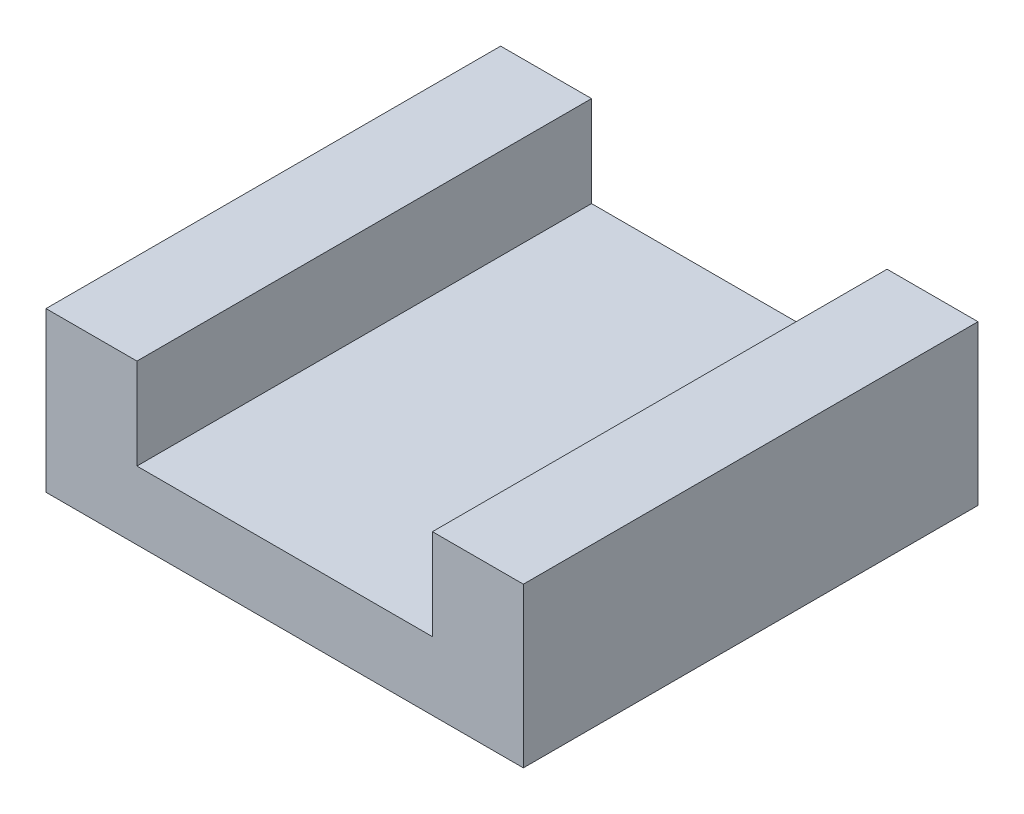
SolidWorks part; units mm, degrees
ref_plane "前基準面" through (0, 0, 0) normal (0, 0, 1) x (1, 0, 0)
ref_plane "上基準面" through (0, 0, 0) normal (0, 1, 0) x (1, 0, 0)
ref_plane "右基準面" through (0, 0, 0) normal (1, 0, 0) x (0, 0, -1)
sketch "草圖1" plane through (0, 0, 0) normal (0, 0, 1) x (1, 0, 0)
  line L0 (3.25, 3.5) -> (5.25, 3.5)
  line L1 (-5.25, 3.5) -> (-3.25, 3.5)
  line L2 (-5.25, 3.5) -> (-5.25, 0)
  line L3 (-5.25, 0) -> (5.25, 0)
  line L4 (5.25, 3.5) -> (5.25, 0)
  line L5 (0, 0) -> (0, 6.2323) construction
  line L6 (-3.25, 3.5) -> (-3.25, 1.5)
  line L7 (-3.25, 1.5) -> (3.25, 1.5)
  line L8 (3.25, 3.5) -> (3.25, 1.5)
  dimension "D1" = 1.5
  dimension "D2" = 6.5
  dimension "D3" = 2
  dimension "D4" = 2
extrude "填料-伸長1" add sketch "草圖1" along normal blind 10
